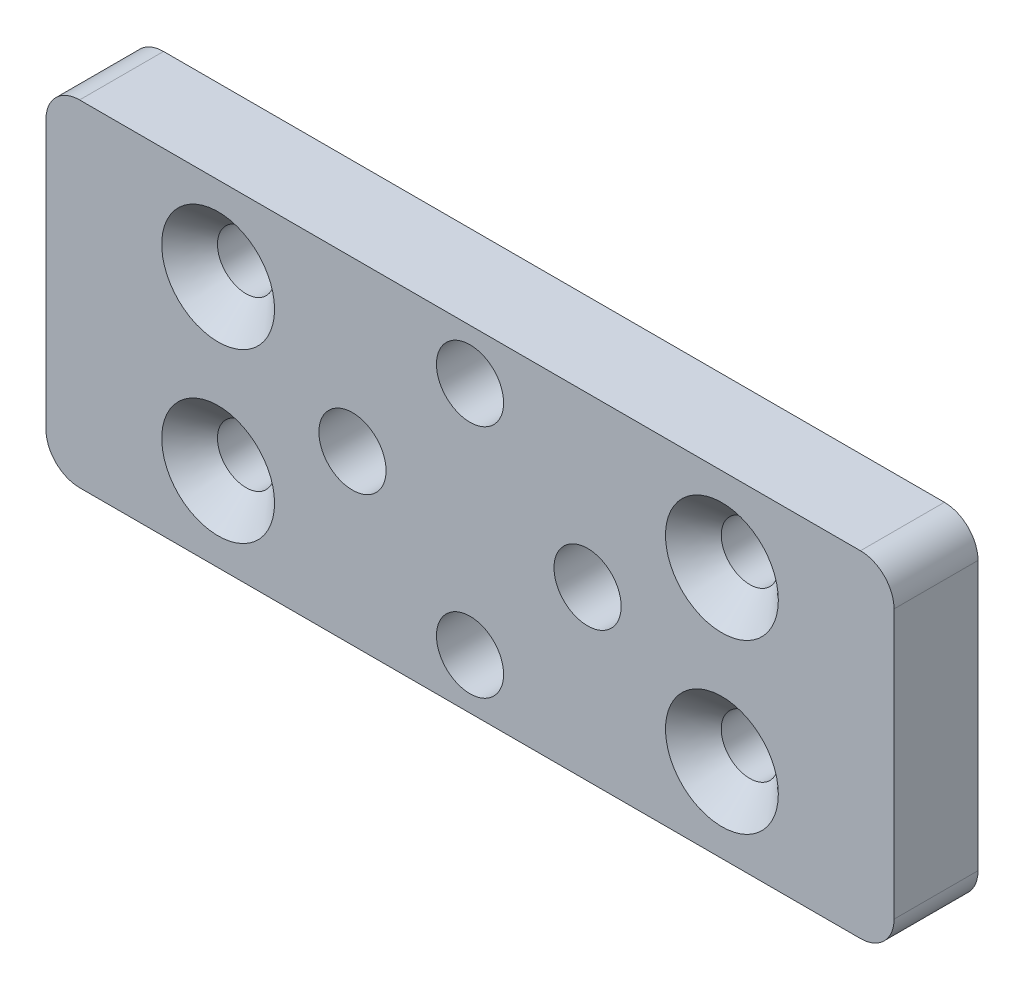
SolidWorks part; units mm, degrees
ref_plane "前视基准面" through (0, 0, 0) normal (0, 0, 1) x (1, 0, 0)
ref_plane "上视基准面" through (0, 0, 0) normal (0, 1, 0) x (1, 0, 0)
ref_plane "右视基准面" through (0, 0, 0) normal (1, 0, 0) x (0, 0, -1)
sketch "草图1" plane through (0, 0, 0) normal (0, 0, 1) x (1, 0, 0)
  line L1 (0, 0) -> (50.5, 0)
  line L2 (0, 0) -> (0, -20)
  line L3 (0, -20) -> (50.5, -20)
  line L4 (50.5, 0) -> (50.5, -20)
  dimension "D1" = 50.5
  dimension "D2" = 20
extrude "凸台-拉伸1" add sketch "草图1" along normal blind 5
sketch "草图2" plane through (0, 0, 0) normal (0, 0, -1) x (-1, 0, 0)
  circle A0 centre (-40.25, -5) radius 1.6
  circle A1 centre (-40.25, -15) radius 1.6
  circle A2 centre (-10.25, -5) radius 1.6
  circle A3 centre (-10.25, -15) radius 1.6
  dimension "D1" = 3.2
extrude "切除-拉伸1" cut sketch "草图2" against normal blind 5
sketch "草图3" plane through (0, 0, 5) normal (0, 0, 1) x (1, 0, 0)
  circle A0 centre (10.25, -5) radius 1.6
  circle A1 centre (10.25, -15) radius 1.6
  circle A2 centre (40.25, -15) radius 1.6
  circle A3 centre (40.25, -5) radius 1.6
hole_wizard "M3 六角凹锥坑螺钉的锥形沉头孔1" positions "草图4" profile "草图5" countersink size "M3" standard "ISO" end condition through all
sketch "草图4" plane through (0, 0, 5) normal (0, 0, 1) x (1, 0, 0)
  point P0 (10.25, -5)
  point P3 (10.25, -15)
  point P6 (40.25, -5)
  point P9 (40.25, -15)
sketch "草图5" plane through (10.25, -5, 5) normal (1, 0, 0) x (0, -1, 0)
  line L0 (0, 0) -> (0, 5)
  line L1 (0, 5) -> (1.7, 5)
  line L2 (1.7, 5) -> (1.7, 1.66)
  line L3 (1.7, 1.66) -> (3.36, 0)
  line L5 (3.36, 0) -> (0, 0)
  line L6 (-1.7, 1.66) -> (-3.36, 0) construction
  line L11 (0, -6.35) -> (0, 107.95) construction
  dimension "通孔孔直径" = 3.4
  dimension "通孔孔深度" = 5
  dimension "近端锥形沉头孔直径" = 6.72
  dimension "近端锥形沉头孔角度" = 90
sketch "草图6" plane through (0, 0, 5) normal (0, 0, 1) x (1, 0, 0)
  line L0 (25.25, -3) -> (25.25, -17) construction
  line L3 (18.25, -10) -> (32.25, -10) construction
  circle A1 centre (25.25, -3) radius 2
  circle A2 centre (32.25, -10) radius 2
  circle A3 centre (18.25, -10) radius 2
  circle A4 centre (25.25, -17) radius 2
  dimension "D2" = 4
extrude "切除-拉伸2" cut sketch "草图6" against normal blind 5
fillet "圆角1" radius 2 4 edges at (50.5, 0, 2.5) (50.5, -20, 2.5) (0, -20, 2.5) (0, 0, 2.5)
